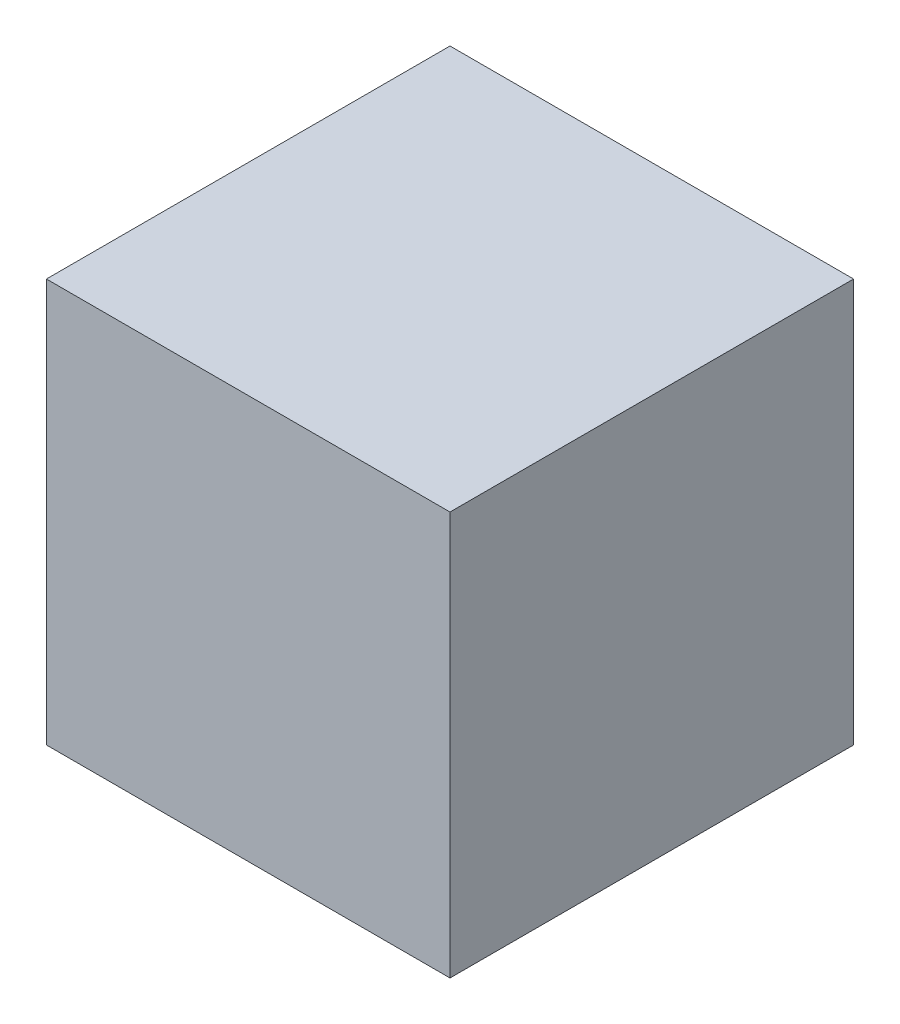
SolidWorks part; units mm, degrees
ref_plane "Front Plane" through (0, 0, 0) normal (0, 0, 1) x (1, 0, 0)
ref_plane "Top Plane" through (0, 0, 0) normal (0, 1, 0) x (1, 0, 0)
ref_plane "Right Plane" through (0, 0, 0) normal (1, 0, 0) x (0, 0, -1)
sketch "Sketch1" plane through (0, 0, 0) normal (0, 1, 0) x (1, 0, 0)
  line L1 (-26.9875, -26.9875) -> (26.9875, -26.9875)
  line L2 (-26.9875, -26.9875) -> (-26.9875, 26.9875)
  line L3 (-26.9875, 26.9875) -> (26.9875, 26.9875)
  line L4 (26.9875, -26.9875) -> (26.9875, 26.9875)
  line L5 (-26.9875, -26.9875) -> (26.9875, 26.9875) construction
  line L6 (-26.9875, 26.9875) -> (26.9875, -26.9875) construction
  point P0 (0, 0)
  dimension "D1" = 53.975
extrude "Boss-Extrude1" add sketch "Sketch1" along normal mid plane 53.975
